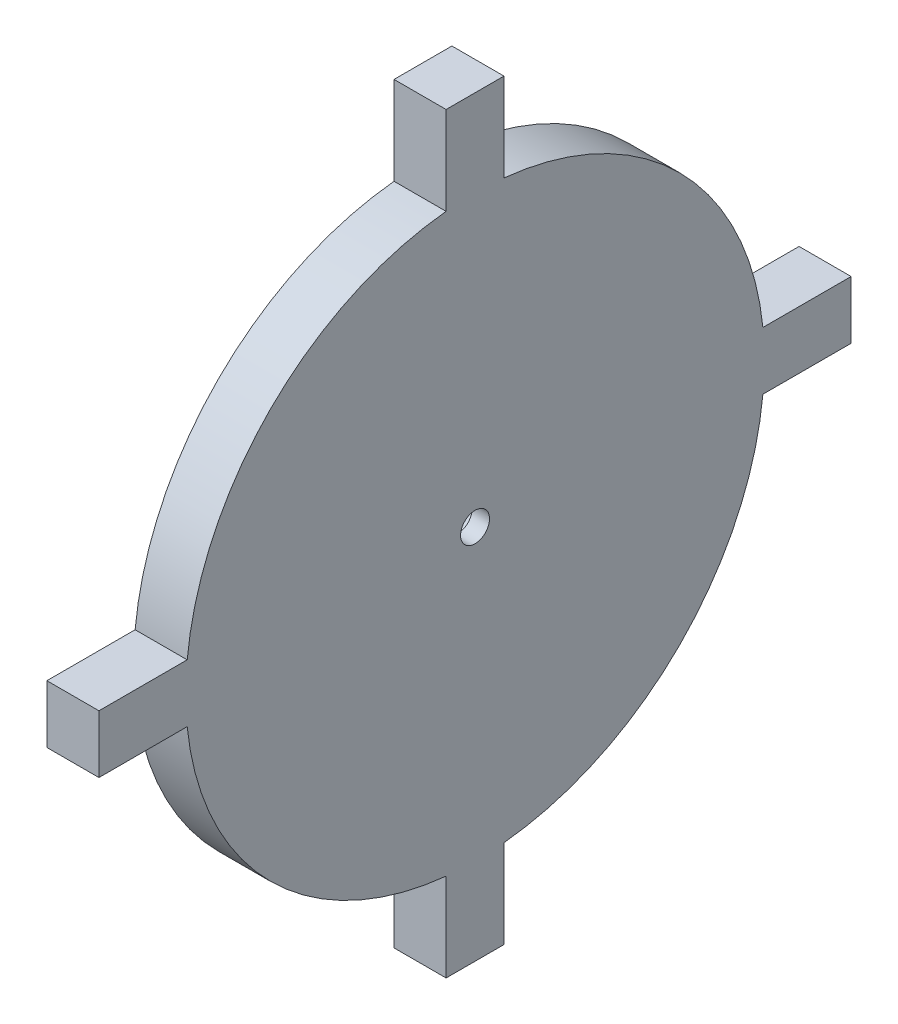
SolidWorks part; units mm, degrees
ref_plane "Front Plane" through (0, 0, 0) normal (0, 0, 1) x (1, 0, 0)
ref_plane "Top Plane" through (0, 0, 0) normal (0, 1, 0) x (1, 0, 0)
ref_plane "Right Plane" through (0, 0, 0) normal (1, 0, 0) x (0, 0, -1)
sketch "Sketch1" plane through (0, 0, 0) normal (1, 0, 0) x (0, 0, -1)
  line L1 (-6.35, 82.55) -> (6.35, 82.55)
  line L2 (-6.35, 82.55) -> (-6.35, -82.55)
  line L3 (-6.35, -82.55) -> (6.35, -82.55)
  line L4 (6.35, 82.55) -> (6.35, -82.55)
  line L5 (-6.35, 82.55) -> (6.35, -82.55) construction
  line L6 (-6.35, -82.55) -> (6.35, 82.55) construction
  line L7 (-82.55, -6.35) -> (82.55, -6.35)
  line L8 (-82.55, -6.35) -> (-82.55, 6.35)
  line L9 (-82.55, 6.35) -> (82.55, 6.35)
  line L10 (82.55, -6.35) -> (82.55, 6.35)
  line L11 (-82.55, -6.35) -> (82.55, 6.35) construction
  line L12 (-82.55, 6.35) -> (82.55, -6.35) construction
  circle A0 centre (0, 0) radius 63.5
  circle A1 centre (0, 0) radius 3.175
  dimension "D1" = 127
  dimension "D6" = 6.35
  dimension "D2" = 12.7
  dimension "D3" = 12.7
  dimension "D4" = 165.1
  dimension "D5" = 165.1
extrude "Boss-Extrude1" add sketch "Sketch1" along normal blind 11.43 contours L9 A0 L4 | A0 L4 L1 L2 | L4 A0 L2 L9 | L2 A0 L9 | A0 L9 L8 L7 | L9 A0 L7 L2 | L7 A0 L2 | L4 A0 L7 | L7 A0 L9 L4 | A0 L7 L10 L9 | L9 L2 L7 L4 | L2 A0 L4 L7 | A0 L2 L3 L4
sketch "Sketch2" plane through (0, 0, 0) normal (-1, 0, 0) x (0, 0, 1)
  line L1 (-9.7282, -0.9706) -> (-4.0235, -8.9101)
  line L2 (-4.0235, -8.9101) -> (5.7046, -7.9395)
  line L3 (5.7046, -7.9395) -> (9.7282, 0.9706)
  line L4 (9.7282, 0.9706) -> (4.0235, 8.9101)
  line L5 (4.0235, 8.9101) -> (-5.7046, 7.9395)
  line L6 (-5.7046, 7.9395) -> (-9.7282, -0.9706)
  circle A0 centre (0, 0) radius 9.7765
  circle A1 centre (0, 0) radius 8.4667 construction
  dimension "D1" = 16.9333
extrude "Cut-Extrude1" cut sketch "Sketch2" against normal blind 7.62 contours A0
